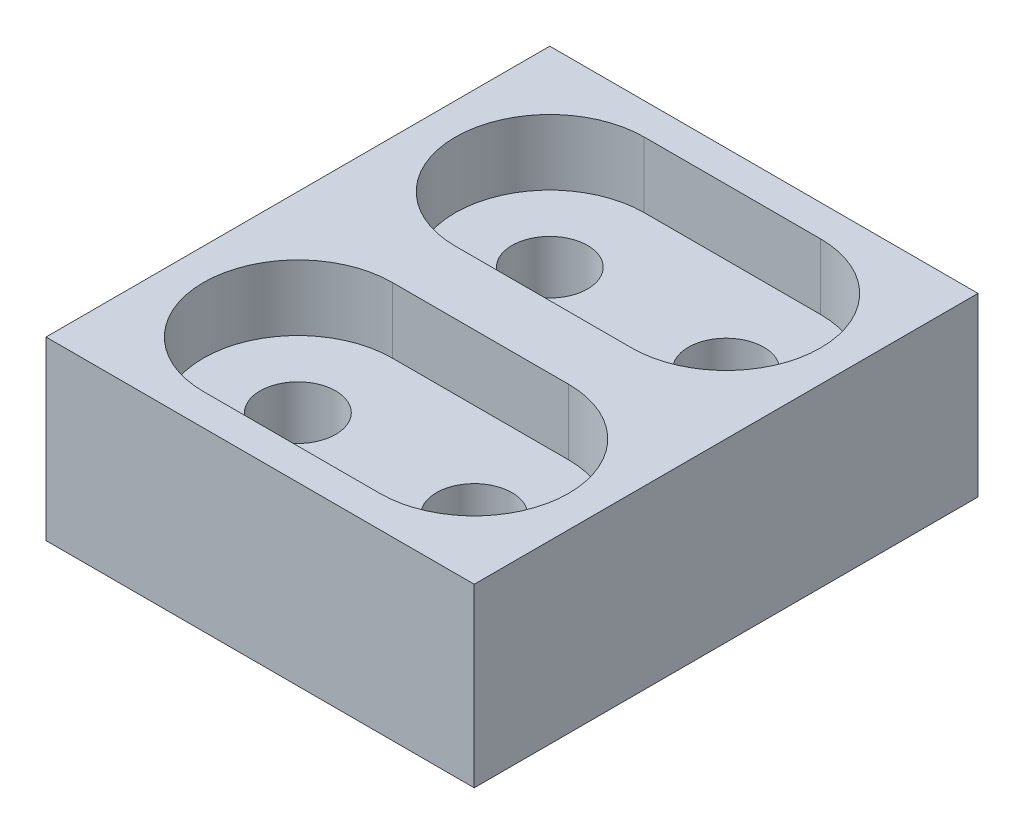
SolidWorks part; units mm, degrees
ref_plane "Front Plane" through (0, 0, 0) normal (0, 0, 1) x (1, 0, 0)
ref_plane "Top Plane" through (0, 0, 0) normal (0, 1, 0) x (1, 0, 0)
ref_plane "Right Plane" through (0, 0, 0) normal (1, 0, 0) x (0, 0, -1)
sketch "Sketch1" plane through (0, 0, 0) normal (0, 1, 0) x (1, 0, 0)
  line L0 (0, 0) -> (0, -10)
  line L1 (0, 0) -> (-7, 0)
  line L2 (-7, 0) -> (-7, -10)
  line L3 (-7, -10) -> (0, -10)
  line L4 (0, 0) -> (5, 0)
  line L5 (0, 0) -> (0, 5)
  line L6 (-7, -10) -> (-7, -15)
  line L7 (-7, -10) -> (-12, -10)
  line L8 (-12, -10) -> (-12, 5)
  line L9 (-12, 5) -> (5, 5)
  line L10 (5, 5) -> (5, -15)
  line L11 (5, -15) -> (-12, -15)
  line L12 (-12, -15) -> (-12, -10)
  circle A0 centre (0, 0) radius 1.5
  circle A1 centre (-7, 0) radius 1.5
  circle A2 centre (-7, -10) radius 1.5
  circle A3 centre (0, -10) radius 1.5
extrude "Boss-Extrude1" add sketch "Sketch1" along normal blind 7 contours A2 L2 A1 L1 A0 L5 L9 L8 L7 | A2 L7 L12 L11 L6 | A3 L3 A2 L6 L11 L10 L4 A0 L0 | A0 L4 L10 L9 L5 | A3 L0 A0 L1 A1 L2 A2 L3
sketch "Sketch2" plane through (0, 7, 0) normal (0, 1, 0) x (1, 0, 0)
  line L0 (-7, -10) -> (-7, -13.75)
  line L1 (-7, -13.75) -> (0, -13.75)
  line L2 (-7, -6.25) -> (0, -6.25)
  line L3 (-7, 3.75) -> (0, 3.75)
  line L4 (-7, -3.75) -> (0, -3.75)
  circle A0 centre (-7, 0) radius 1.5 construction
  circle A1 centre (0, 0) radius 1.5 construction
  circle A2 centre (-7, -10) radius 1.5 construction
  circle A3 centre (0, -10) radius 1.5 construction
  circle A4 centre (0, -10) radius 1.5
  circle A5 centre (-7, -10) radius 1.5
  circle A6 centre (0, 0) radius 1.5
  circle A7 centre (-7, 0) radius 1.5
  circle A8 centre (-7, 0) radius 3.75
  circle A9 centre (0, 0) radius 3.75
  circle A10 centre (-7, -10) radius 3.75
  circle A11 centre (0, -10) radius 3.75
extrude "Cut-Extrude6" cut sketch "Sketch2" against normal blind 2.6
